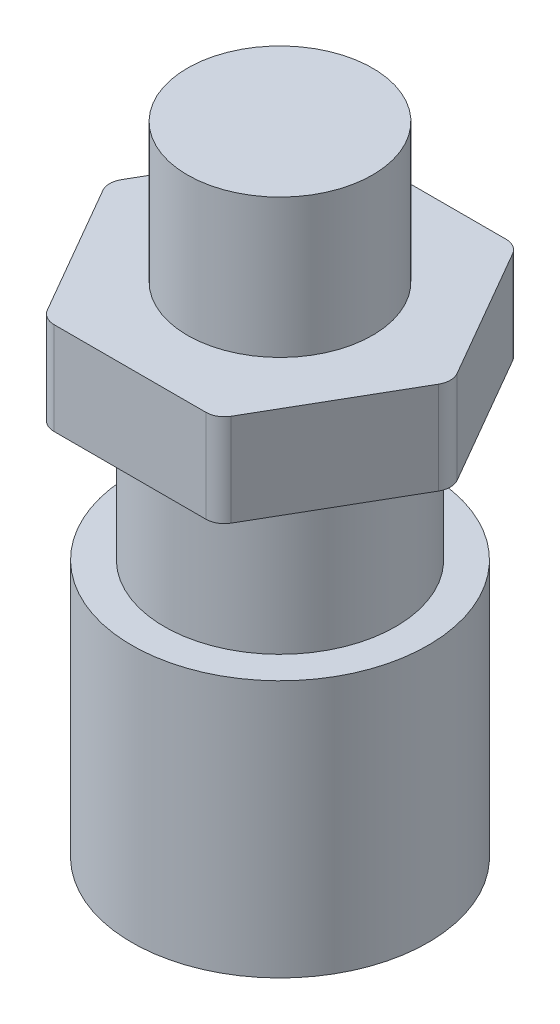
SolidWorks part; units mm, degrees
ref_plane "Front Plane" through (0, 0, 0) normal (0, 0, 1) x (1, 0, 0)
ref_plane "Top Plane" through (0, 0, 0) normal (0, 1, 0) x (1, 0, 0)
ref_plane "Right Plane" through (0, 0, 0) normal (1, 0, 0) x (0, 0, -1)
sketch "Sketch1" plane through (0, 0, 0) normal (0, 1, 0) x (1, 0, 0)
  line L0 (-20.574, 0) -> (20.574, 0) construction
  line L1 (-10.287, 17.8176) -> (10.287, -17.8176) construction
  line L2 (10.287, 17.8176) -> (-10.287, -17.8176) construction
  line L3 (20.574, 0) -> (-20.574, 0) construction
  line L4 (10.287, -17.8176) -> (-10.287, 17.8176) construction
  line L5 (-10.287, -17.8176) -> (10.287, 17.8176) construction
  line L6 (-11.8784, 20.574) -> (11.8784, 20.574)
  line L7 (11.8784, 20.574) -> (23.7568, 0)
  line L8 (23.7568, 0) -> (11.8784, -20.574)
  line L9 (11.8784, -20.574) -> (-11.8784, -20.574)
  line L10 (-11.8784, -20.574) -> (-23.7568, 0)
  line L11 (-23.7568, 0) -> (-11.8784, 20.574)
  circle A0 centre (0, 0) radius 20.574 construction
  point P17 (0, 0)
  dimension "D1" = 41.148
  dimension "D2" = 6
extrude "Boss-Extrude1" add sketch "Sketch1" along normal blind 12.7
fillet "Fillet1" radius 2.54 6 edges at (-11.8784, 6.35, 20.574) (-23.7568, 6.35, 0) (-11.8784, 6.35, -20.574) (11.8784, 6.35, -20.574) (11.8784, 6.35, 20.574) (23.7568, 6.35, 0)
sketch "Sketch2" plane through (0, 0, 0) normal (0, -1, 0) x (1, 0, 0)
  circle A0 centre (0, 0) radius 20.32
  dimension "D1" = 40.64
extrude "Boss-Extrude4" add sketch "Sketch2" along normal blind 55.626
sketch "Sketch4" plane through (0, 0, 0) normal (0, -1, 0) x (1, 0, 0)
  line L6 (10.4119, 20.574) -> (-10.4119, 20.574)
  line L7 (-12.6116, 19.304) -> (-23.0236, 1.27)
  line L8 (-23.0236, -1.27) -> (-12.6116, -19.304)
  line L9 (-10.4119, -20.574) -> (10.4119, -20.574)
  line L10 (12.6116, -19.304) -> (23.0236, -1.27)
  line L11 (23.0236, 1.27) -> (12.6116, 19.304)
  line L12 (10.4119, 20.574) -> (-10.4119, 20.574)
  line L13 (-12.6116, 19.304) -> (-23.0236, 1.27)
  line L14 (-23.0236, -1.27) -> (-12.6116, -19.304)
  line L15 (-10.4119, -20.574) -> (10.4119, -20.574)
  line L16 (12.6116, -19.304) -> (23.0236, -1.27)
  line L17 (23.0236, 1.27) -> (12.6116, 19.304)
  circle A0 centre (0, 0) radius 20.32 construction
  circle A1 centre (0, 0) radius 20.32
  circle A2 centre (0, 0) radius 15.875
  arc A6 (-10.4119, 20.574) -> (-12.6116, 19.304) centre (-10.4119, 18.034) ccw
  arc A7 (-23.0236, 1.27) -> (-23.0236, -1.27) centre (-20.8239, 0) ccw
  arc A8 (-12.6116, -19.304) -> (-10.4119, -20.574) centre (-10.4119, -18.034) ccw
  arc A9 (10.4119, -20.574) -> (12.6116, -19.304) centre (10.4119, -18.034) ccw
  arc A10 (23.0236, -1.27) -> (23.0236, 1.27) centre (20.8239, 0) ccw
  arc A11 (12.6116, 19.304) -> (10.4119, 20.574) centre (10.4119, 18.034) ccw
  arc A12 (-10.4119, 20.574) -> (-12.6116, 19.304) centre (-10.4119, 18.034) ccw
  arc A13 (-23.0236, 1.27) -> (-23.0236, -1.27) centre (-20.8239, 0) ccw
  arc A14 (-12.6116, -19.304) -> (-10.4119, -20.574) centre (-10.4119, -18.034) ccw
  arc A15 (10.4119, -20.574) -> (12.6116, -19.304) centre (10.4119, -18.034) ccw
  arc A16 (23.0236, -1.27) -> (23.0236, 1.27) centre (20.8239, 0) ccw
  arc A17 (12.6116, 19.304) -> (10.4119, 20.574) centre (10.4119, 18.034) ccw
  circle M13 centre (0, 0) radius 20.32
  dimension "D2" = 31.75
  dimension "D1" = 0
extrude "Cut-Extrude1" cut sketch "Sketch4" along normal blind 20.32 contours A2 M13
sketch "Sketch5" plane through (0, 12.7, 0) normal (0, 1, 0) x (1, 0, 0)
  circle A0 centre (0, 0) radius 12.7
  dimension "D1" = 25.4
extrude "Boss-Extrude5" add sketch "Sketch5" along normal blind 19.05
